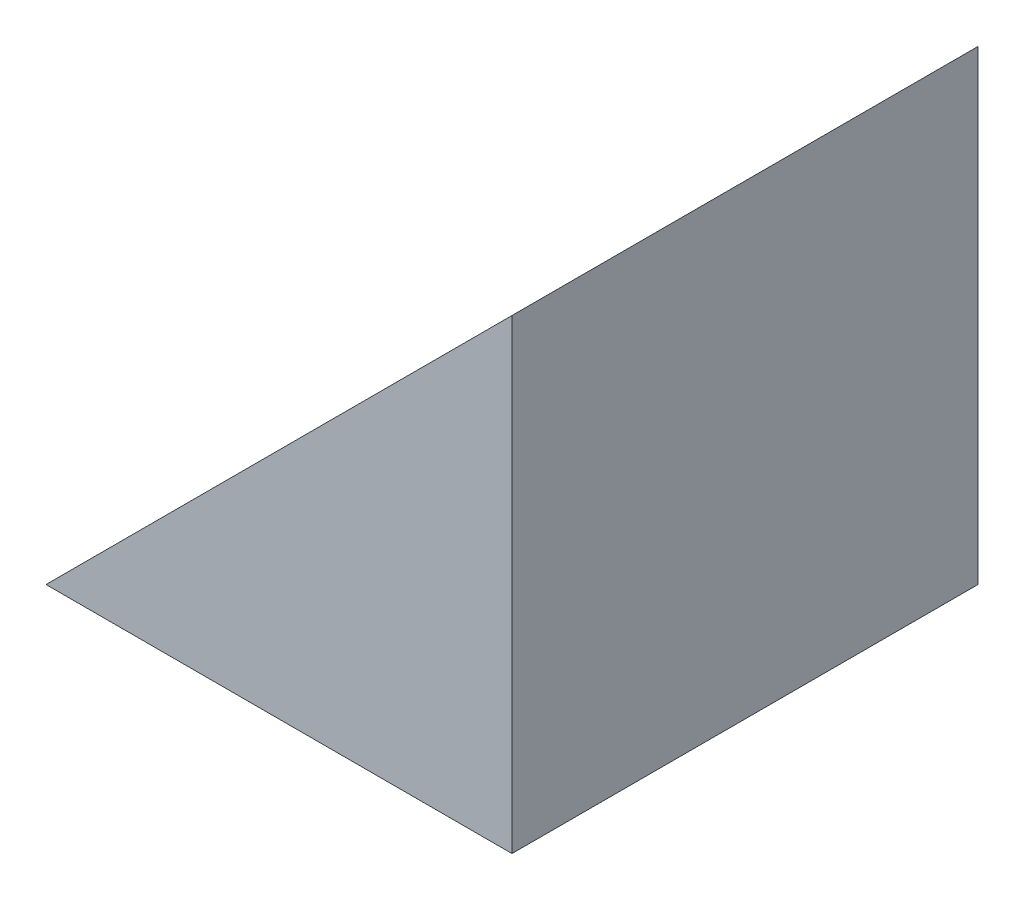
SolidWorks part; units mm, degrees
ref_plane "前视基准面" through (0, 0, 0) normal (0, 0, 1) x (1, 0, 0)
ref_plane "上视基准面" through (0, 0, 0) normal (0, 1, 0) x (1, 0, 0)
ref_plane "右视基准面" through (0, 0, 0) normal (1, 0, 0) x (0, 0, -1)
sketch "草图1" plane through (0, 0, 0) normal (0, 0, 1) x (1, 0, 0)
  line L0 (17.4714, 13.2779) -> (17.4714, 18.2779)
  line L1 (17.4714, 13.2779) -> (12.4714, 13.2779)
  line L2 (12.4714, 13.2779) -> (17.4714, 18.2779)
  dimension "D1" = 5
  dimension "D2" = 5
extrude "凸台-拉伸1" add sketch "草图1" along normal blind 5
